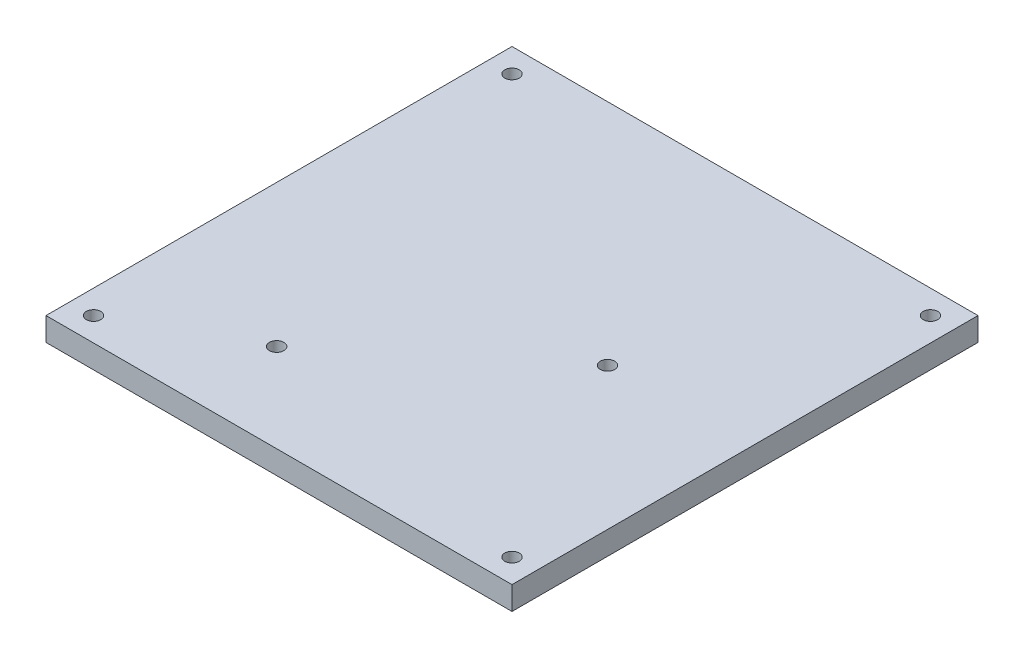
SolidWorks part; units mm, degrees
ref_plane "Front Plane" through (0, 0, 0) normal (0, 0, 1) x (1, 0, 0)
ref_plane "Top Plane" through (0, 0, 0) normal (0, 1, 0) x (1, 0, 0)
ref_plane "Right Plane" through (0, 0, 0) normal (1, 0, 0) x (0, 0, -1)
sketch "Sketch1" plane through (0, 0, 0) normal (0, 1, 0) x (1, 0, 0)
  line L1 (-50, -50) -> (50, -50)
  line L2 (-50, -50) -> (-50, 50)
  line L3 (-50, 50) -> (50, 50)
  line L4 (50, -50) -> (50, 50)
  line L5 (-50, -50) -> (50, 50) construction
  line L6 (-50, 50) -> (50, -50) construction
  circle A0 centre (-44.9, 44.9) radius 1.55
  circle A1 centre (44.9, 44.9) radius 1.55
  circle A2 centre (44.9, -44.9) radius 1.55
  circle A3 centre (-44.9, -44.9) radius 1.55
  circle A23 centre (-19.5, -31) radius 1.55
  circle A24 centre (19.5, 1) radius 1.55
  point P0 (0, 0)
  point P8 (0, 0)
  point P9 (15, 0)
  point P11 (0, 0)
  point P14 (0, 0)
  point P17 (0, 0)
  point P20 (0, 0)
  point P23 (15, 0)
  point P35 (0, 0)
  point P41 (15, 0)
  dimension "D3" = 3.1
  dimension "D5" = 5.1
  dimension "D6" = 3.1
  dimension "D8" = 3.1
  dimension "D1" = 100
  dimension "D2" = 100
  dimension "D4" = 4
extrude "Boss-Extrude1" add sketch "Sketch1" along normal blind 5
